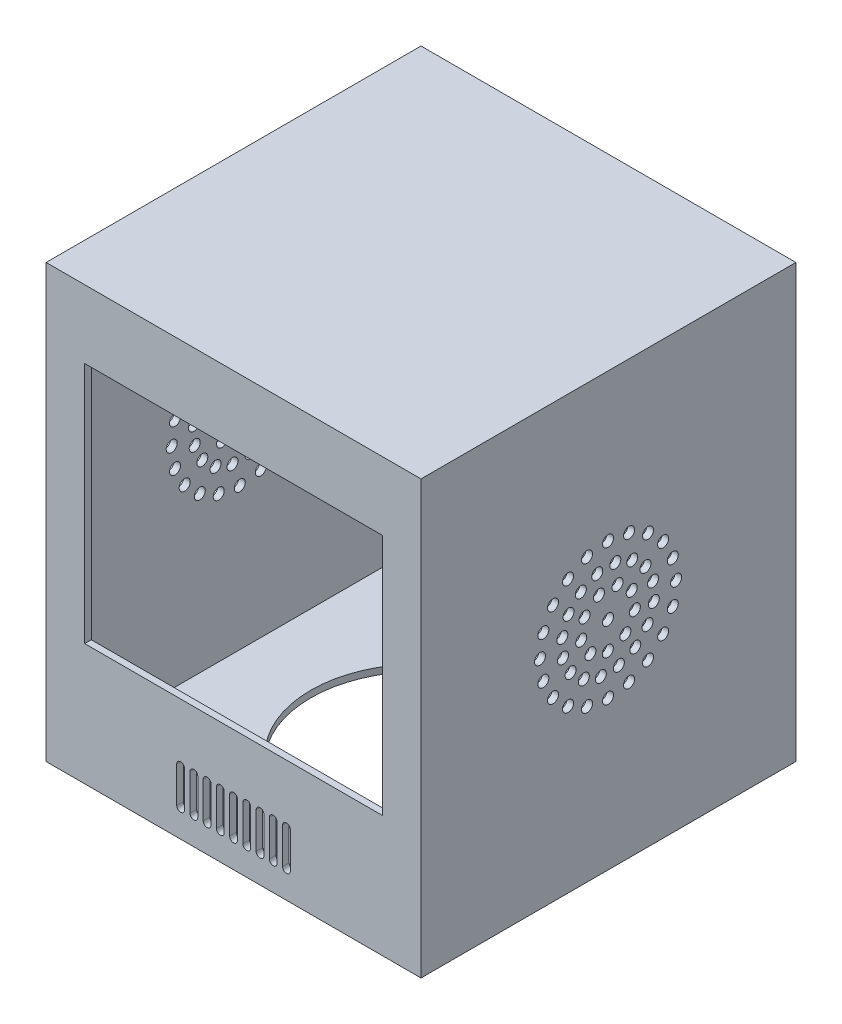
SolidWorks part; units mm, degrees
ref_plane "Front Plane" through (0, 0, 0) normal (0, 0, 1) x (1, 0, 0)
ref_plane "Top Plane" through (0, 0, 0) normal (0, 1, 0) x (1, 0, 0)
ref_plane "Right Plane" through (0, 0, 0) normal (1, 0, 0) x (0, 0, -1)
sketch "Sketch1" plane through (0, 0, 0) normal (0, 1, 0) x (1, 0, 0)
  line L1 (-85, 85) -> (85, 85)
  line L2 (-85, 85) -> (-85, -85)
  line L3 (-85, -85) -> (85, -85)
  line L4 (85, 85) -> (85, -85)
  line L5 (-85, 85) -> (85, -85) construction
  line L6 (-85, -85) -> (85, 85) construction
  line L11 (-80.2336, 80.2336) -> (30.2336, -30.2336) construction
  line L12 (-55.2336, -55.2336) -> (55.2336, 55.2336) construction
  line L13 (-82, 82) -> (82, 82)
  line L14 (-82, 82) -> (-82, -82)
  line L15 (-82, -82) -> (82, -82)
  line L16 (82, 82) -> (82, -82)
  line L17 (-82, 82) -> (82, -82) construction
  line L18 (-82, -82) -> (82, 82) construction
  point P0 (0, 0)
  point P6 (0, 0)
  point P11 (0, 0)
  dimension "D1" = 170
  dimension "D2" = 170
  dimension "D3" = 164
extrude "Boss-Extrude1" add sketch "Sketch1" along normal blind 190
sketch "Sketch2" plane through (0, 0, 85) normal (0, 0, 1) x (1, 0, 0)
  line L1 (-67.5, 162.0699) -> (67.5, 162.0699)
  line L2 (-67.5, 162.0699) -> (-67.5, 52.0699)
  line L3 (-67.5, 52.0699) -> (67.5, 52.0699)
  line L4 (67.5, 162.0699) -> (67.5, 52.0699)
  line L5 (-67.5, 162.0699) -> (67.5, 52.0699) construction
  line L6 (-67.5, 52.0699) -> (67.5, 162.0699) construction
  point P0 (0, 107.0699)
  dimension "D1" = 110
  dimension "D2" = 135
extrude "Cut-Extrude2" cut sketch "Sketch2" against normal blind 19
sketch "Sketch3" plane through (0, 0, 0) normal (0, -1, 0) x (1, 0, 0)
  line L1 (-85, 85) -> (85, 85)
  line L2 (-85, 85) -> (-85, -85)
  line L3 (-85, -85) -> (85, -85)
  line L4 (85, 85) -> (85, -85)
  line L5 (-85, 85) -> (85, -85) construction
  line L6 (-85, -85) -> (85, 85) construction
  point P0 (0, 0)
extrude "Boss-Extrude3" add sketch "Sketch3" along normal blind 3
sketch "Sketch4" plane through (0, 190, 0) normal (0, 1, 0) x (1, 0, 0)
  line L1 (-85, 85) -> (85, 85)
  line L2 (-85, 85) -> (-85, -85)
  line L3 (-85, -85) -> (85, -85)
  line L4 (85, 85) -> (85, -85)
  line L5 (-85, 85) -> (85, -85) construction
  line L6 (-85, -85) -> (85, 85) construction
  point P0 (0, 0)
extrude "Boss-Extrude4" add sketch "Sketch4" along normal blind 3
sketch "Sketch6" plane through (85, 0, 0) normal (1, 0, 0) x (0, 0, -1)
  line L0 (-85, 193) -> (85, -3) construction
  line L1 (-0.1831, 126.2232) -> (9.3522, 124.713) construction
  line L2 (9.3522, 124.713) -> (-0.1831, 95.3662) construction
  line L3 (4.5846, 125.4681) -> (-0.1831, 95.3662) construction
  line L4 (10.7894, 113.2717) -> (-0.1831, 95.3662) construction
  circle A49 centre (-0.1831, 95.3662) radius 2.5
  circle A50 centre (-0.1831, 95.3662) radius 35 construction
  circle A51 centre (-0.1831, 126.2232) radius 2.5
  circle A52 centre (9.3522, 124.713) radius 2.5
  circle A53 centre (17.9542, 120.3301) radius 2.5
  circle A54 centre (24.7808, 113.5035) radius 2.5
  circle A55 centre (29.1637, 104.9016) radius 2.5
  circle A56 centre (30.6739, 95.3662) radius 2.5
  circle A57 centre (29.1637, 85.8309) radius 2.5
  circle A58 centre (24.7808, 77.2289) radius 2.5
  circle A59 centre (17.9542, 70.4024) radius 2.5
  circle A60 centre (9.3522, 66.0194) radius 2.5
  circle A61 centre (-0.1831, 64.5092) radius 2.5
  circle A62 centre (-9.7184, 66.0194) radius 2.5
  circle A63 centre (-18.3204, 70.4024) radius 2.5
  circle A64 centre (-25.147, 77.2289) radius 2.5
  circle A65 centre (-29.5299, 85.8309) radius 2.5
  circle A66 centre (-31.0401, 95.3662) radius 2.5
  circle A67 centre (-29.5299, 104.9016) radius 2.5
  circle A68 centre (-25.147, 113.5035) radius 2.5
  circle A69 centre (-18.3204, 120.3301) radius 2.5
  circle A70 centre (-9.7184, 124.713) radius 2.5
  circle A71 centre (-0.1831, 95.3662) radius 21 construction
  circle A72 centre (3.102, 116.1077) radius 2.5
  circle A73 centre (10.7894, 113.2717) radius 2.5
  circle A74 centre (16.8063, 107.7097) radius 2.5
  circle A75 centre (20.2367, 100.2686) radius 2.5
  circle A76 centre (20.5584, 92.0811) radius 2.5
  circle A77 centre (17.7223, 84.3937) radius 2.5
  circle A78 centre (12.1604, 78.3769) radius 2.5
  circle A79 centre (4.7192, 74.9464) radius 2.5
  circle A80 centre (-3.4682, 74.6248) radius 2.5
  circle A81 centre (-11.1556, 77.4608) radius 2.5
  circle A82 centre (-17.1725, 83.0227) radius 2.5
  circle A83 centre (-20.6029, 90.4639) radius 2.5
  circle A84 centre (-20.9246, 98.6513) radius 2.5
  circle A85 centre (-18.0885, 106.3387) radius 2.5
  circle A86 centre (-12.5266, 112.3556) radius 2.5
  circle A87 centre (-5.0855, 115.786) radius 2.5
  circle A88 centre (-0.1831, 95.3662) radius 12.3435 construction
  circle A89 centre (4.1369, 106.9291) radius 2.5
  circle A90 centre (10.5587, 101.447) radius 2.5
  circle A91 centre (11.9542, 93.1197) radius 2.5
  circle A92 centre (7.6706, 85.8436) radius 2.5
  circle A93 centre (-0.2879, 83.0232) radius 2.5
  circle A94 centre (-8.1973, 85.9782) radius 2.5
  circle A95 centre (-12.3568, 93.326) radius 2.5
  circle A96 centre (-10.8201, 101.6284) radius 2.5
  circle A97 centre (-4.3062, 107.0007) radius 2.5
  point P51 (-0.1831, 95.3662)
  point P91 (-0.1831, 95.3662)
  point P103 (-0.1831, 95.3662)
extrude "Cut-Extrude3" cut sketch "Sketch6" against normal through all
sketch "Sketch7" plane through (0, 0, 85) normal (0, 0, 1) x (1, 0, 0)
  line L0 (0, 25.6482) -> (0, 9.3516) construction
  line L1 (1.7671, 25.6482) -> (1.7671, 9.3516)
  line L2 (-1.7671, 25.6482) -> (-1.7671, 9.3516)
  line L3 (-53.7984, 17.4999) -> (55.7618, 17.4999) construction
  line L4 (6, 25.6482) -> (6, 9.3516) construction
  line L5 (7.7671, 25.6482) -> (7.7671, 9.3516)
  line L6 (4.2329, 25.6482) -> (4.2329, 9.3516)
  line L7 (12, 25.6482) -> (12, 9.3516) construction
  line L8 (13.7671, 25.6482) -> (13.7671, 9.3516)
  line L9 (10.2329, 25.6482) -> (10.2329, 9.3516)
  line L10 (18, 25.6482) -> (18, 9.3516) construction
  line L11 (19.7671, 25.6482) -> (19.7671, 9.3516)
  line L12 (16.2329, 25.6482) -> (16.2329, 9.3516)
  line L13 (24, 25.6482) -> (24, 9.3516) construction
  line L14 (25.7671, 25.6482) -> (25.7671, 9.3516)
  line L15 (22.2329, 25.6482) -> (22.2329, 9.3516)
  line L16 (-6, 25.6482) -> (-6, 9.3516) construction
  line L17 (-4.2329, 25.6482) -> (-4.2329, 9.3516)
  line L18 (-7.7671, 25.6482) -> (-7.7671, 9.3516)
  line L19 (-12, 25.6482) -> (-12, 9.3516) construction
  line L20 (-10.2329, 25.6482) -> (-10.2329, 9.3516)
  line L21 (-13.7671, 25.6482) -> (-13.7671, 9.3516)
  line L22 (-18, 25.6482) -> (-18, 9.3516) construction
  line L23 (-16.2329, 25.6482) -> (-16.2329, 9.3516)
  line L24 (-19.7671, 25.6482) -> (-19.7671, 9.3516)
  line L25 (-24, 25.6482) -> (-24, 9.3516) construction
  line L26 (-22.2329, 25.6482) -> (-22.2329, 9.3516)
  line L27 (-25.7671, 25.6482) -> (-25.7671, 9.3516)
  arc A0 (1.7671, 25.6482) -> (-1.7671, 25.6482) centre (0, 25.6482) ccw
  arc A1 (-1.7671, 9.3516) -> (1.7671, 9.3516) centre (0, 9.3516) ccw
  arc A2 (7.7671, 25.6482) -> (4.2329, 25.6482) centre (6, 25.6482) ccw
  arc A3 (4.2329, 9.3516) -> (7.7671, 9.3516) centre (6, 9.3516) ccw
  arc A4 (13.7671, 25.6482) -> (10.2329, 25.6482) centre (12, 25.6482) ccw
  arc A5 (10.2329, 9.3516) -> (13.7671, 9.3516) centre (12, 9.3516) ccw
  arc A6 (19.7671, 25.6482) -> (16.2329, 25.6482) centre (18, 25.6482) ccw
  arc A7 (16.2329, 9.3516) -> (19.7671, 9.3516) centre (18, 9.3516) ccw
  arc A8 (25.7671, 25.6482) -> (22.2329, 25.6482) centre (24, 25.6482) ccw
  arc A9 (22.2329, 9.3516) -> (25.7671, 9.3516) centre (24, 9.3516) ccw
  arc A10 (-4.2329, 25.6482) -> (-7.7671, 25.6482) centre (-6, 25.6482) ccw
  arc A11 (-7.7671, 9.3516) -> (-4.2329, 9.3516) centre (-6, 9.3516) ccw
  arc A12 (-10.2329, 25.6482) -> (-13.7671, 25.6482) centre (-12, 25.6482) ccw
  arc A13 (-13.7671, 9.3516) -> (-10.2329, 9.3516) centre (-12, 9.3516) ccw
  arc A14 (-16.2329, 25.6482) -> (-19.7671, 25.6482) centre (-18, 25.6482) ccw
  arc A15 (-19.7671, 9.3516) -> (-16.2329, 9.3516) centre (-18, 9.3516) ccw
  arc A16 (-22.2329, 25.6482) -> (-25.7671, 25.6482) centre (-24, 25.6482) ccw
  arc A17 (-25.7671, 9.3516) -> (-22.2329, 9.3516) centre (-24, 9.3516) ccw
  point P3 (0, 17.4999)
  point P14 (6, 17.4999)
  point P21 (12, 17.4999)
  point P28 (18, 17.4999)
  point P35 (24, 17.4999)
  point P42 (-6, 17.4999)
  point P49 (-12, 17.4999)
  point P56 (-18, 17.4999)
  point P63 (-24, 17.4999)
  dimension "D1" = 5
  dimension "D2" = 5
extrude "Cut-Extrude4" cut sketch "Sketch7" against normal blind 32
sketch "Sketch9" plane through (0, -3, 0) normal (0, -1, 0) x (1, 0, 0)
  circle A0 centre (0, 0) radius 50
  dimension "D1" = 100
extrude "Cut-Extrude5" cut sketch "Sketch9" against normal blind 38 contours A0
